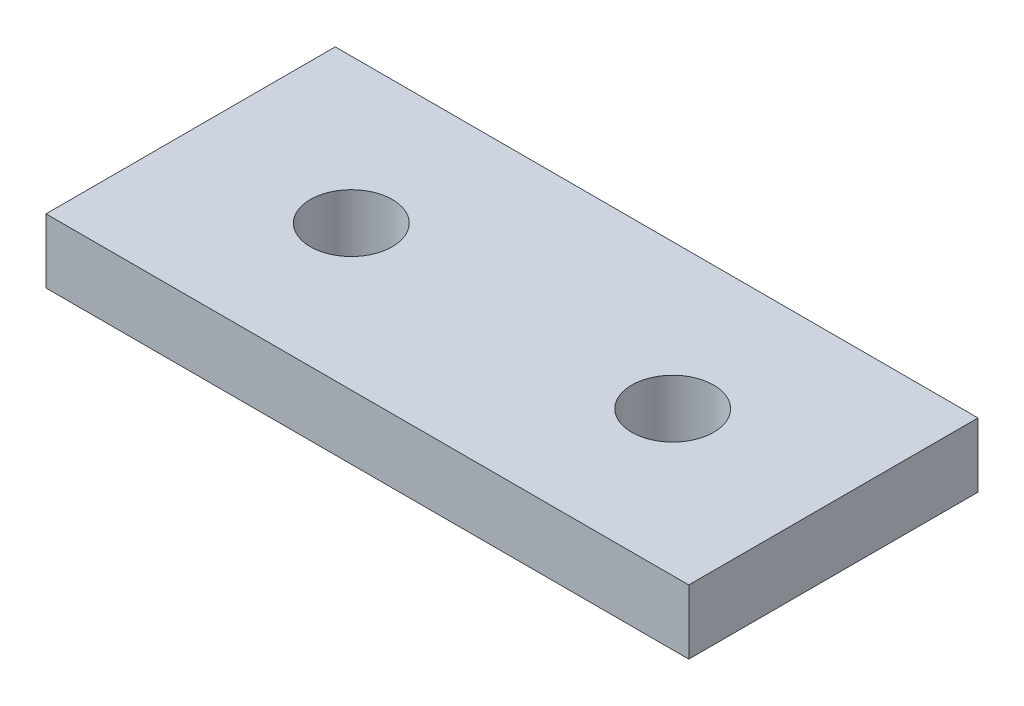
SolidWorks part; units mm, degrees
material "6061-T6 (SS)"
ref_plane "Front Plane" through (0, 0, 0) normal (0, 0, 1) x (1, 0, 0)
ref_plane "Top Plane" through (0, 0, 0) normal (0, 1, 0) x (1, 0, 0)
ref_plane "Right Plane" through (0, 0, 0) normal (1, 0, 0) x (0, 0, -1)
sketch "Sketch1" plane through (0, 0, 0) normal (0, 1, 0) x (1, 0, 0)
  line L0 (0, 0) -> (0, 9) construction
  line L1 (20, -9) -> (-20, -9)
  line L2 (20, -9) -> (20, 9)
  line L3 (20, 9) -> (-20, 9)
  line L4 (-20, -9) -> (-20, 9)
  line L5 (20, -9) -> (-20, 9) construction
  line L6 (20, 9) -> (-20, -9) construction
  circle A0 centre (-10, 0) radius 2.55
  circle A1 centre (10, 0) radius 2.55
  point P0 (0, 0)
  dimension "D3" = 5.1
  dimension "D1" = 18
  dimension "D2" = 40
  dimension "D4" = 20
extrude "Boss-Extrude1" add sketch "Sketch1" along normal blind 4
